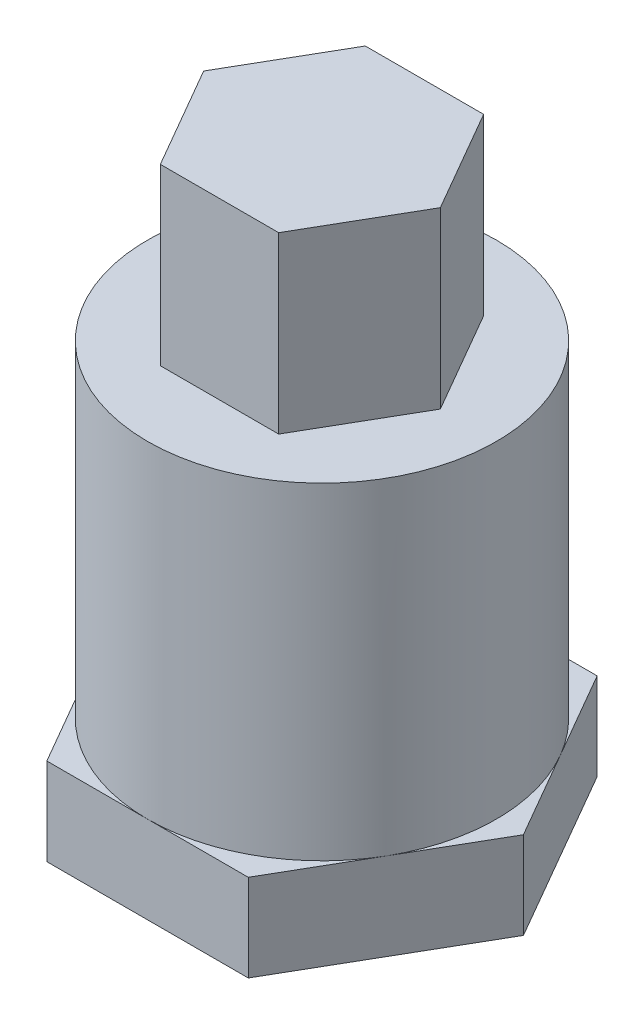
SolidWorks part; units mm, degrees
ref_plane "Front Plane" through (0, 0, 0) normal (0, 0, 1) x (1, 0, 0)
ref_plane "Top Plane" through (0, 0, 0) normal (0, 1, 0) x (1, 0, 0)
ref_plane "Right Plane" through (0, 0, 0) normal (1, 0, 0) x (0, 0, -1)
sketch "Sketch1" plane through (0, 0, 0) normal (0, 1, 0) x (1, 0, 0)
  line L1 (5.4271, 0) -> (2.7135, 4.7)
  line L2 (2.7135, 4.7) -> (-2.7135, 4.7)
  line L3 (-2.7135, 4.7) -> (-5.4271, 0)
  line L4 (-5.4271, 0) -> (-2.7135, -4.7)
  line L5 (-2.7135, -4.7) -> (2.7135, -4.7)
  line L6 (2.7135, -4.7) -> (5.4271, 0)
  circle A0 centre (0, 0) radius 4.7 construction
  dimension "D1" = 9.4
extrude "Boss-Extrude1" add sketch "Sketch1" along normal blind 8
sketch "Sketch2" plane through (0, 0, 0) normal (0, -1, 0) x (1, 0, 0)
  circle A0 centre (0, 0) radius 8
  dimension "D1" = 16
extrude "Boss-Extrude2" add sketch "Sketch2" along normal blind 15
sketch "Sketch3" plane through (0, -15, 0) normal (0, -1, 0) x (1, 0, 0)
  circle A0 centre (0, 0) radius 23
  circle A1 centre (0, 0) radius 8 construction
  dimension "D1" = 15
extrude "Boss-Extrude3" add sketch "Sketch3" along normal blind 7
sketch "Sketch4" plane through (0, -22, 0) normal (0, -1, 0) x (1, 0, 0)
  line L1 (10.1614, 0) -> (-10.1614, 0) construction
  arc A0 (-24.8365, -2.8544) -> (-24.8365, 2.8544) centre (0, 0) cw construction
  arc A2 (-28.876, -2.6786) -> (-28.876, 2.6786) centre (0, 0) cw
  arc A3 (-28.8104, -3.3111) -> (-28.8104, 3.3111) centre (0, 0) cw construction
  spline S0 degree 3 poles (-28.876, 2.6786) (-27.341, 2.7837) (-21.4523, 3.0394) (-17.8705, 2.2022) (-15.9721, 0.5752) (-15.3766, 0) knots -0.203879 -0.203879 -0.203879 -0.203879 0 0.695602 1 1 1 1
  spline S1 degree 3 poles (-28.876, -2.6786) (-27.341, -2.7837) (-21.4523, -3.0394) (-17.8705, -2.2022) (-15.9721, -0.5752) (-15.3766, 0) knots -0.203879 -0.203879 -0.203879 -0.203879 0 0.695602 1 1 1 1
  dimension "D1" = 4
extrude "Cut-Extrude1" cut sketch "Sketch4" against normal blind 1 draft 45
fillet "Fillet2" radius 1 5 edges at (-22.8819, -21.5002, -2.3277) (-22.9013, -21.3001, 2.1282) (-23, -21, 0) (-18.9133, -21, 1.1779) (-21.1533, -21, -1.6856)
pattern_circular "CirPattern1" count 6 every 45 about axis through (0, -22, 0) along (0, 1, 0) of "Cut-Extrude1", "Fillet2"
sketch "Sketch5" plane through (0, -22, 0) normal (0, -1, 0) x (1, 0, 0)
  line L0 (-245.0554, -113.5226) -> (-245.0554, 81.9035) construction
  line L1 (0, -8.8) -> (0, 8.8) construction
  line L2 (-2.4074, -8.5668) -> (0, -10.6858)
  line L3 (0, 0.7457) -> (0, -10.6858) construction
  line L4 (2.4074, -8.5668) -> (0, -10.6858)
  spline S0 degree 1 poles (0, 0.7457) (-1.3665, 0.4718) knots 0 0 1 1
  spline S1 degree 1 poles (-1.3665, 0.4718) (-1.3494, -3.2772) knots 0 0 1 1
  spline S2 degree 3 poles (-1.3494, -3.2772) (-1.3228, -3.6344) (-1.1267, -4.1271) (-0.5986, -4.7724) (-0.2808, -5.1322) (0, -5.2972) knots 0 0 0 0 0.426063 0.616527 1 1 1 1
  spline S3 degree 3 poles (0, -6.811) (-0.5392, -6.4577) (-1.5601, -5.8942) (-2.516, -4.9333) (-2.9812, -4.1673) (-3.0132, -3.6202) (-3.016, -2.9456) (-2.9244, -2.1331) (-2.9103, -1.235) (-2.9092, -0.5693) (-2.9169, -0.011) (-3.1423, 0.6239) (-3.9909, 1.3241) (-5.2481, 2.0904) (-7.1532, 3.0787) (-8.9464, 3.8242) (-10.0759, 4.9012) (-10.5938, 5.8364) (-10.9217, 7.5348) (-10.9529, 8.9951) (-10.8334, 9.9239) knots 0 0 0 0 0.087818 0.156578 0.182085 0.206742 0.229318 0.273952 0.31724 0.351103 0.364287 0.392873 0.438837 0.509184 0.593709 0.730008 0.768263 0.802813 0.873163 1 1 1 1
  spline S4 degree 3 poles (-10.8334, 9.9239) (-11.243, 8.989) (-11.5419, 7.2897) (-11.6073, 5.0204) (-10.8157, 3.4928) (-9.6001, 2.669) (-8.1759, 1.7345) (-6.8872, 0.7533) (-5.7466, -0.2777) (-4.9296, -1.2509) (-4.9868, -2.1695) (-5.0027, -2.5385) knots 0 0 0 0 0.195889 0.33973 0.432671 0.517106 0.622276 0.767275 0.830917 0.925849 1 1 1 1
  spline S5 degree 3 poles (-5.0027, -2.5385) (-5.0233, -2.9907) (-5.3087, -3.4748) (-5.458, -4.4324) (-4.9971, -4.887) (-4.6741, -5.0396) knots 0 0 0 0 0.464937 0.585419 1 1 1 1
  spline S6 degree 3 poles (-4.6741, -5.0396) (-4.4706, -5.1519) (-3.98, -5.6073) (-3.2765, -6.1305) (-2.738, -6.7386) (-2.5993, -7.1771) (-2.6139, -7.784) (-2.7415, -8.3109) (-2.4074, -8.5668) knots 0 0 0 0 0.15475 0.447524 0.589127 0.691519 0.745256 1 1 1 1
  spline S7 degree 1 poles (0, 0.7457) (1.3665, 0.4718) knots 0 0 1 1
  spline S8 degree 1 poles (1.3665, 0.4718) (1.3494, -3.2772) knots 0 0 1 1
  spline S9 degree 3 poles (1.3494, -3.2772) (1.3228, -3.6344) (1.1267, -4.1271) (0.5986, -4.7724) (0.2808, -5.1322) (0, -5.2972) knots 0 0 0 0 0.426063 0.616527 1 1 1 1
  spline S10 degree 3 poles (0, -6.811) (0.5392, -6.4577) (1.5601, -5.8942) (2.516, -4.9333) (2.9812, -4.1673) (3.0132, -3.6202) (3.016, -2.9456) (2.9244, -2.1331) (2.9103, -1.235) (2.9092, -0.5693) (2.9169, -0.011) (3.1423, 0.6239) (3.9909, 1.3241) (5.2481, 2.0904) (7.1532, 3.0787) (8.9464, 3.8242) (10.0759, 4.9012) (10.5938, 5.8364) (10.9217, 7.5348) (10.9529, 8.9951) (10.8334, 9.9239) knots 0 0 0 0 0.087818 0.156578 0.182085 0.206742 0.229318 0.273952 0.31724 0.351103 0.364287 0.392873 0.438837 0.509184 0.593709 0.730008 0.768263 0.802813 0.873163 1 1 1 1
  spline S11 degree 3 poles (10.8334, 9.9239) (11.243, 8.989) (11.5419, 7.2897) (11.6073, 5.0204) (10.8157, 3.4928) (9.6001, 2.669) (8.1759, 1.7345) (6.8872, 0.7533) (5.7466, -0.2777) (4.9296, -1.2509) (4.9868, -2.1695) (5.0027, -2.5385) knots 0 0 0 0 0.195889 0.33973 0.432671 0.517106 0.622276 0.767275 0.830917 0.925849 1 1 1 1
  spline S12 degree 3 poles (5.0027, -2.5385) (5.0233, -2.9907) (5.3087, -3.4748) (5.458, -4.4324) (4.9971, -4.887) (4.6741, -5.0396) knots 0 0 0 0 0.464937 0.585419 1 1 1 1
  spline S13 degree 3 poles (4.6741, -5.0396) (4.4706, -5.1519) (3.98, -5.6073) (3.2765, -6.1305) (2.738, -6.7386) (2.5993, -7.1771) (2.6139, -7.784) (2.7415, -8.3109) (2.4074, -8.5668) knots 0 0 0 0 0.15475 0.447524 0.589127 0.691519 0.745256 1 1 1 1
  text T0 "B.o.B" font "Steamwreck" height in points 30
extrude "Cut-Extrude2" cut sketch "Sketch5" against normal blind 1
sketch "Sketch7" plane through (0, -15, 0) normal (0, 1, 0) x (1, 0, 0)
  circle A0 centre (0, 0) radius 24.8704
extrude "Cut-Extrude3" cut sketch "Sketch7" against normal through all
sketch "Sketch8" plane through (0, -15, 0) normal (0, -1, 0) x (1, 0, 0)
  line L1 (9.2376, 0) -> (4.6188, 8)
  line L2 (4.6188, 8) -> (-4.6188, 8)
  line L3 (-4.6188, 8) -> (-9.2376, 0)
  line L4 (-9.2376, 0) -> (-4.6188, -8)
  line L5 (-4.6188, -8) -> (4.6188, -8)
  line L6 (4.6188, -8) -> (9.2376, 0)
  circle A0 centre (0, 0) radius 8 construction
  dimension "D1" = 16
extrude "Boss-Extrude10" add sketch "Sketch8" along normal blind 4 contours L4 L5 L6 L1 L2 L3
